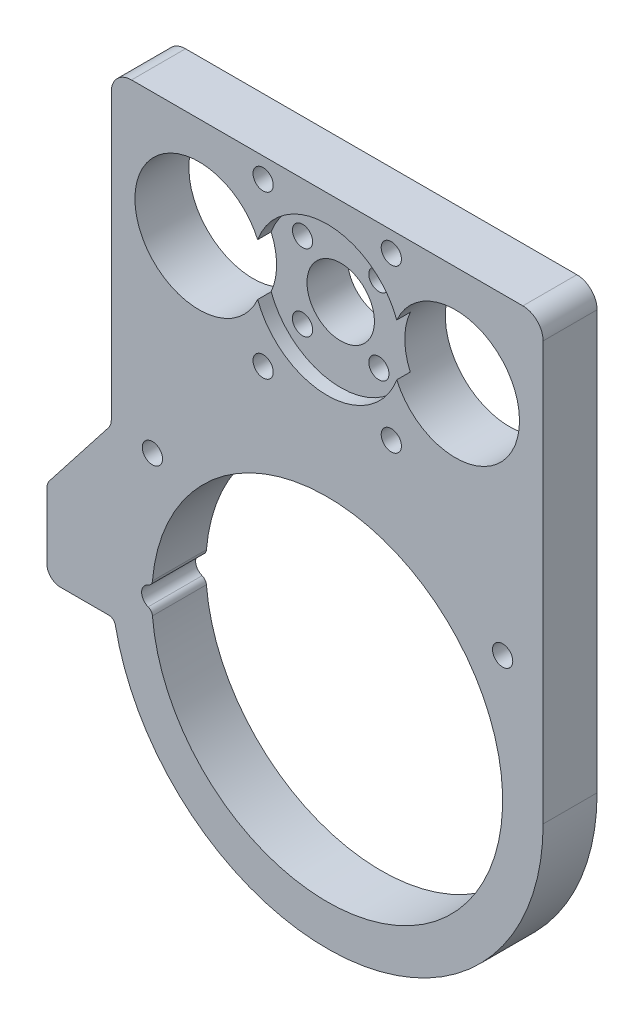
SolidWorks part; units mm, degrees
ref_plane "Спереди" through (0, 0, 0) normal (0, 0, 1) x (1, 0, 0)
ref_plane "Сверху" through (0, 0, 0) normal (0, 1, 0) x (1, 0, 0)
ref_plane "Справа" through (0, 0, 0) normal (1, 0, 0) x (0, 0, -1)
sketch "Эскиз1" plane through (0, 0, 0) normal (0, 0, 1) x (1, 0, 0)
  line L0 (32, -50) -> (32, -17)
  line L2 (-32, -17) -> (-32, 12)
  line L3 (-29, 15) -> (29, 15)
  line L4 (32, -17) -> (32, 12)
  line L5 (-41.544, -52.6838) -> (-41.544, -43.7154)
  line L6 (-41.1197, -42.4838) -> (-32.4242, -31.359)
  line L7 (-32, -30.1273) -> (-32, -17)
  line L9 (-41.544, -52.6838) -> (-41.544, -53.383)
  line L10 (-39.544, -55.383) -> (-32.3768, -55.383)
  circle A0 centre (0, 0) radius 5
  circle A1 centre (-19, 0) radius 9.5
  circle A2 centre (19, 0) radius 9.5
  arc A4 (29, 15) -> (32, 12) centre (29, 12) cw
  arc A5 (-32, 12) -> (-29, 15) centre (-29, 12) cw
  arc A6 (-25.9028, -52.2464) -> (-25.9028, -47.7536) centre (0, -50) ccw
  arc A7 (-31.3957, -56.1896) -> (32, -50) centre (0, -50) ccw
  arc A10 (-41.544, -53.383) -> (-39.544, -55.383) centre (-39.544, -53.383) ccw
  arc A11 (-32.3768, -55.383) -> (-31.3957, -56.1896) centre (-32.3768, -56.383) cw
  arc A12 (-26.5394, -48.6003) -> (-26.5394, -51.3997) centre (-26, -50) ccw
  arc A13 (-26.5394, -51.3997) -> (-25.9028, -52.2464) centre (-26.899, -52.3328) cw
  arc A14 (-26.5394, -48.6003) -> (-25.9028, -47.7536) centre (-26.899, -47.6672) ccw
  arc A19 (-41.544, -43.7154) -> (-41.1197, -42.4838) centre (-39.544, -43.7154) cw
  arc A20 (-32, -30.1273) -> (-32.4242, -31.359) centre (-34, -30.1273) cw
  point P33 (-41.544, -55.383)
  point P36 (-31.544, -55.383)
  point P54 (0, 0)
  circle B0 centre (0, 0) radius 8 construction
  circle B1 centre (-5.6569, 5.6569) radius 1.5
  circle B2 centre (5.6569, 5.6569) radius 1.5
  circle B3 centre (5.6569, -5.6569) radius 1.5
  circle B4 centre (-5.6569, -5.6569) radius 1.5
  circle B5 centre (-9.5, 12) radius 1.5
  circle B6 centre (9.5, 12) radius 1.5
  circle B7 centre (9.5, -12) radius 1.5
  circle B8 centre (-9.5, -12) radius 1.5
  circle B9 centre (-25.9028, -31.359) radius 1.5
  circle B10 centre (26, -31.359) radius 1.5
  dimension "D1" = 19
  dimension "D3" = 10
  dimension "D4" = 19
  dimension "D5" = 19
  dimension "D6" = 64
  dimension "D9" = 3
  dimension "D10" = 52
  dimension "D12" = 9.1672
  dimension "D7" = 2
  dimension "D2" = 19
  dimension "D8" = 15
  dimension "D11" = 50
sketch_block_instance "Блок1-1"
sketch_block "Блок1" parameters "D1"=3, "D2"=1.25
sketch_block_instance "Блок2-1"
sketch_block "Блок2"
extrude "Бобышка-Вытянуть1" add sketch "Эскиз1" along normal blind 8
sketch "Эскиз2" plane through (0, 0, 8) normal (0, 0, 1) x (1, 0, 0)
  circle A0 centre (0, 0) radius 11
extrude "Вырез-Вытянуть1" cut sketch "Эскиз2" against normal blind 2
